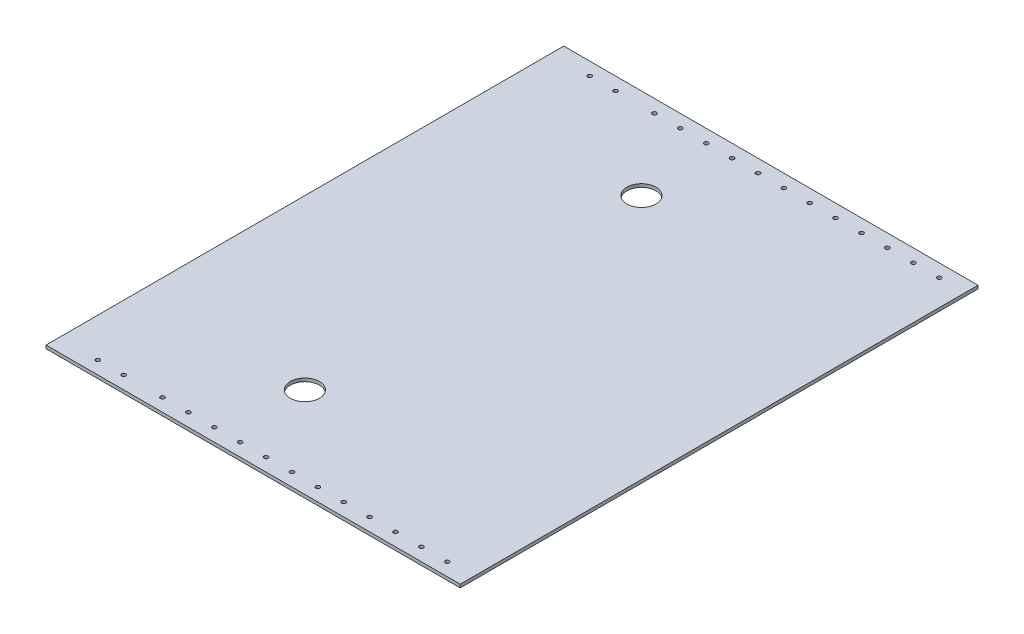
SolidWorks part; units mm, degrees
material "Lexan"
ref_plane "Front Plane" through (0, 0, 0) normal (0, 0, 1) x (1, 0, 0)
ref_plane "Top Plane" through (0, 0, 0) normal (0, 1, 0) x (1, 0, 0)
ref_plane "Right Plane" through (0, 0, 0) normal (1, 0, 0) x (0, 0, -1)
sketch "Sketch1" plane through (0, 0, 0) normal (0, 1, 0) x (1, 0, 0)
  line L1 (0, 0) -> (571.5, 0)
  line L2 (0, 0) -> (0, 508)
  line L3 (0, 508) -> (571.5, 508)
  line L4 (571.5, 0) -> (571.5, 508)
  dimension "D1" = 571.5
  dimension "D2" = 508
extrude "Boss-Extrude1" add sketch "Sketch1" along normal blind 3.175
sketch "Sketch2" plane through (0, 3.175, 0) normal (0, 1, 0) x (1, 0, 0)
  line L0 (273.05, 419.1) -> (273.05, 508) construction
  line L1 (215.9, 419.1) -> (330.2, 419.1) construction
  line L3 (215.9, 88.9) -> (330.2, 88.9) construction
  line L4 (571.5, 0) -> (571.5, 508) construction
  line L5 (571.5, 508) -> (0, 508) construction
  line L6 (273.05, 88.9) -> (273.05, 0) construction
  line L7 (0, 0) -> (571.5, 0) construction
  circle A1 centre (330.2, 419.1) radius 14.2875
  circle A3 centre (330.2, 88.9) radius 14.2875
  dimension "D1" = 114.3
  dimension "D2" = 28.575
  dimension "D3" = 241.3
  dimension "D4" = 28.575
  dimension "D7" = 330.2
  dimension "D8" = 241.3
extrude "Cut-Extrude1" cut sketch "Sketch2" against normal blind 3.175
sketch "Sketch4" plane through (0, 3.175, 0) normal (0, 1, 0) x (1, 0, 0)
  line L0 (571.5, 495.3) -> (0, 495.3) construction
  line L1 (571.5, 0) -> (571.5, 508) construction
  line L2 (0, 508) -> (0, 0) construction
  line L3 (571.5, 508) -> (0, 508) construction
  line L4 (0, 254) -> (571.5, 254) construction
  line L5 (571.5, 12.7) -> (0, 12.7) construction
  circle A0 centre (546.1, 495.3) radius 2.0193
  circle A1 centre (520.7, 495.3) radius 2.0193
  circle A2 centre (495.3, 495.3) radius 2.0193
  circle A3 centre (469.9, 495.3) radius 2.0193
  circle A4 centre (444.5, 495.3) radius 2.0193
  circle A5 centre (419.1, 495.3) radius 2.0193
  circle A6 centre (393.7, 495.3) radius 2.0193
  circle A7 centre (368.3, 495.3) radius 2.0193
  circle A8 centre (342.9, 495.3) radius 2.0193
  circle A9 centre (317.5, 495.3) radius 2.0193
  circle A10 centre (292.1, 495.3) radius 2.0193
  circle A11 centre (266.7, 495.3) radius 2.0193
  circle A12 centre (228.6, 495.3) radius 2.0193
  circle A13 centre (203.2, 495.3) radius 2.0193
  circle A14 centre (203.2, 12.7) radius 2.0193
  circle A15 centre (228.6, 12.7) radius 2.0193
  circle A16 centre (266.7, 12.7) radius 2.0193
  circle A17 centre (292.1, 12.7) radius 2.0193
  circle A18 centre (317.5, 12.7) radius 2.0193
  circle A19 centre (342.9, 12.7) radius 2.0193
  circle A20 centre (368.3, 12.7) radius 2.0193
  circle A21 centre (393.7, 12.7) radius 2.0193
  circle A22 centre (419.1, 12.7) radius 2.0193
  circle A23 centre (444.5, 12.7) radius 2.0193
  circle A24 centre (469.9, 12.7) radius 2.0193
  circle A25 centre (495.3, 12.7) radius 2.0193
  circle A26 centre (520.7, 12.7) radius 2.0193
  circle A27 centre (546.1, 12.7) radius 2.0193
  dimension "D2" = 4.0386
  dimension "D3" = 25.4
  dimension "D5" = 38.1
  dimension "D6" = 25.4
  dimension "D1" = 12.7
  dimension "D4" = 12
extrude "Cut-Extrude3" cut sketch "Sketch4" against normal through all both
sketch "Sketch5" plane through (0, 0, 0) normal (-1, 0, 0) x (0, 0, 1)
  line L1 (-567.431, 71.2281) -> (52.1486, 71.2281)
  line L2 (-567.431, 71.2281) -> (-567.431, -17.807)
  line L3 (-567.431, -17.807) -> (52.1486, -17.807)
  line L4 (52.1486, 71.2281) -> (52.1486, -17.807)
extrude "Cut-Extrude4" cut sketch "Sketch5" against normal blind 165.1
